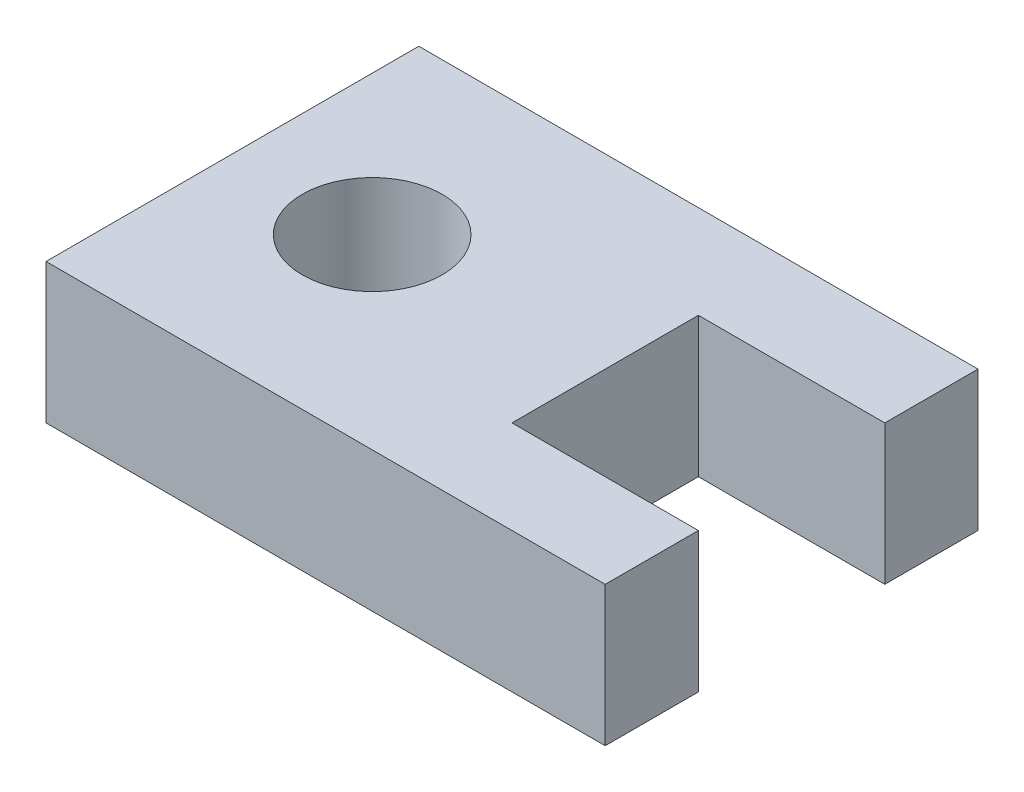
SolidWorks part; units mm, degrees
ref_plane "Front Plane" through (0, 0, 0) normal (0, 0, 1) x (1, 0, 0)
ref_plane "Top Plane" through (0, 0, 0) normal (0, 1, 0) x (1, 0, 0)
ref_plane "Right Plane" through (0, 0, 0) normal (1, 0, 0) x (0, 0, -1)
sketch "Sketch1" plane through (0, 0, 0) normal (0, 1, 0) x (1, 0, 0)
  line L0 (0, 20) -> (0, -20) construction
  line L1 (-30, 20) -> (30, 20)
  line L2 (-30, 20) -> (-30, -20)
  line L3 (-30, -20) -> (30, -20)
  line L4 (30, 20) -> (30, -20)
  line L5 (-30, 0) -> (30, 0) construction
  point P8 (0, 0)
  dimension "D1" = 60
  dimension "D2" = 40
extrude "Boss-Extrude1" add sketch "Sketch1" along normal blind 15
sketch "Sketch2" plane through (0, 15, 0) normal (0, 1, 0) x (1, 0, 0)
  line L0 (-30, 20) -> (-30, -20) construction
  line L1 (-30, -20) -> (30, -20) construction
  circle A0 centre (-15, 0) radius 7.5
  dimension "D2" = 15
  dimension "D1" = 15
  dimension "D3" = 20
extrude "Cut-Extrude1" cut sketch "Sketch2" against normal up to next
sketch "Sketch3" plane through (0, 15, 0) normal (0, 1, 0) x (1, 0, 0)
  line L0 (30, -20) -> (30, 20) construction
  line L1 (30, 10) -> (10, 10)
  line L2 (30, 10) -> (30, -10)
  line L3 (30, -10) -> (10, -10)
  line L4 (10, 10) -> (10, -10)
  line L5 (30, 20) -> (-30, 20) construction
  dimension "D1" = 20
  dimension "D2" = 20
  dimension "D3" = 10
extrude "Cut-Extrude2" cut sketch "Sketch3" against normal up to next
